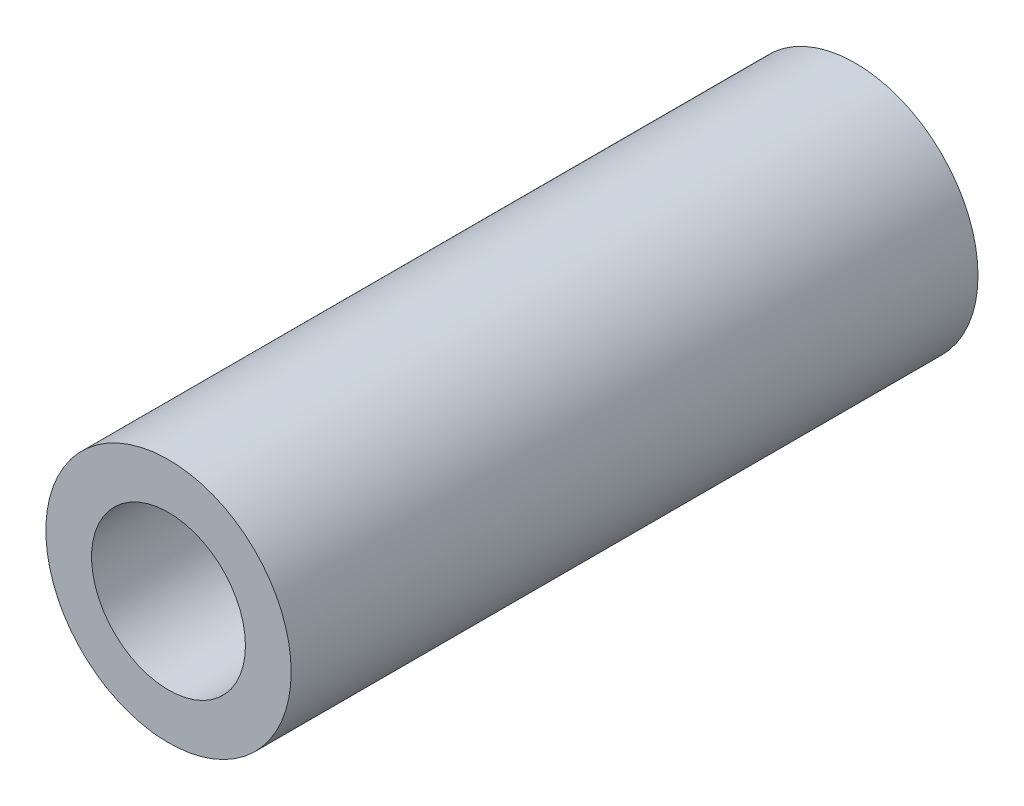
SolidWorks part; units mm, degrees
material "6061-T6 (SS)"
ref_plane "Front Plane" through (0, 0, 0) normal (0, 0, 1) x (1, 0, 0)
ref_plane "Top Plane" through (0, 0, 0) normal (0, 1, 0) x (1, 0, 0)
ref_plane "Right Plane" through (0, 0, 0) normal (1, 0, 0) x (0, 0, -1)
sketch "Sketch1" plane through (0, 0, 0) normal (0, 0, 1) x (1, 0, 0)
  circle A0 centre (0, 0) radius 2.4892
  circle A1 centre (0, 0) radius 3.9688
  dimension "D1" = 4.9784
  dimension "D2" = 7.9375
extrude "Boss-Extrude1" add sketch "Sketch1" along normal blind 22.225 contours A1 A0
